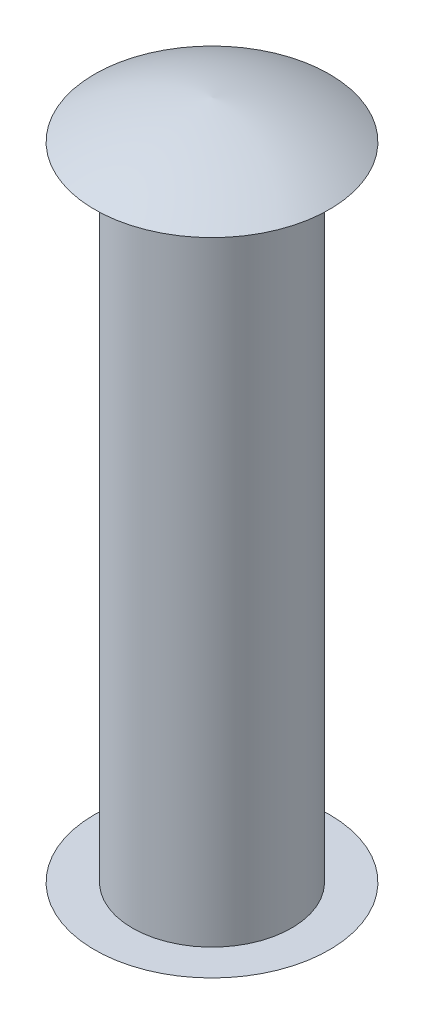
SolidWorks part; units mm, degrees
ref_plane "Front Plane" through (0, 0, 0) normal (0, 0, 1) x (1, 0, 0)
ref_plane "Top Plane" through (0, 0, 0) normal (0, 1, 0) x (1, 0, 0)
ref_plane "Right Plane" through (0, 0, 0) normal (1, 0, 0) x (0, 0, -1)
sketch "Sketch1" plane through (0, 0, 0) normal (0, 1, 0) x (1, 0, 0)
  circle A0 centre (0, 0) radius 3.175
  dimension "D1" = 6.35
extrude "Boss-Extrude1" add sketch "Sketch1" along normal mid plane 25.5778
sketch "Sketch3" plane through (0, 0, 0) normal (0, 0, 1) x (1, 0, 0)
  line L0 (3.175, 12.7889) -> (-3.175, 12.7889) construction
  line L1 (0, 12.7889) -> (-4.6812, 12.7889)
  line L2 (0, 12.7889) -> (0, 14.3129)
  spline S0 degree 2 poles (-4.6812, 12.7889) (-2.4857, 14.0675) (0, 14.3129) knots 0 0 0 1 1 1
  point P4 (-1.4072, 13.744)
  point P5 (0, 0)
  point P10 (-1.4072, 13.8049)
  dimension "D1" = 1.524
  dimension "D2" = 4.6812
  dimension "D3" = 1.27
  dimension "D4" = 1.524
revolve "Revolve1" add sketch "Sketch3" angle 360 about L2
mirror "Mirror1" about plane through (0, 0, 0) normal (0, 1, 0) of "Revolve1"
